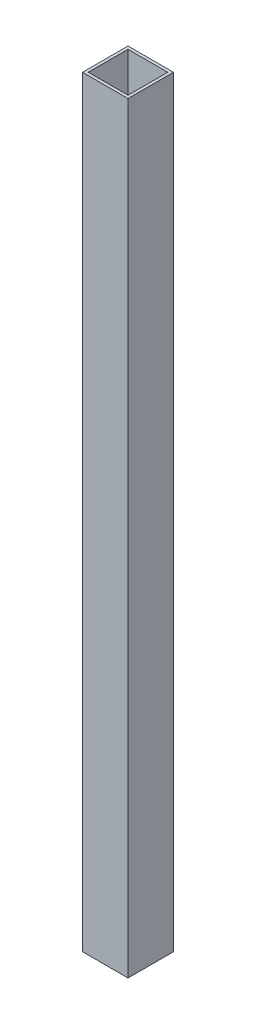
SolidWorks part; units mm, degrees
material "6061 Alloy"
ref_plane "Front Plane" through (0, 0, 0) normal (0, 0, 1) x (1, 0, 0)
ref_plane "Top Plane" through (0, 0, 0) normal (0, 1, 0) x (1, 0, 0)
ref_plane "Right Plane" through (0, 0, 0) normal (1, 0, 0) x (0, 0, -1)
sketch "Sketch1" plane through (0, 0, 0) normal (0, 1, 0) x (1, 0, 0)
  line L0 (22.225, -22.225) -> (22.225, 22.225)
  line L1 (25.4, -25.4) -> (-25.4, -25.4)
  line L2 (25.4, -25.4) -> (25.4, 25.4)
  line L3 (25.4, 25.4) -> (-25.4, 25.4)
  line L4 (-25.4, -25.4) -> (-25.4, 25.4)
  line L5 (25.4, -25.4) -> (-25.4, 25.4) construction
  line L6 (25.4, 25.4) -> (-25.4, -25.4) construction
  line L7 (22.225, 22.225) -> (-22.225, 22.225)
  line L8 (-22.225, -22.225) -> (-22.225, 22.225)
  line L9 (22.225, -22.225) -> (-22.225, -22.225)
  point P0 (0, 0)
  dimension "D1" = 50.8
  dimension "D2" = 50.8
  dimension "D3" = 3.175
extrude "Boss-Extrude1" add sketch "Sketch1" along normal up to surface (850.9002 mm away)
